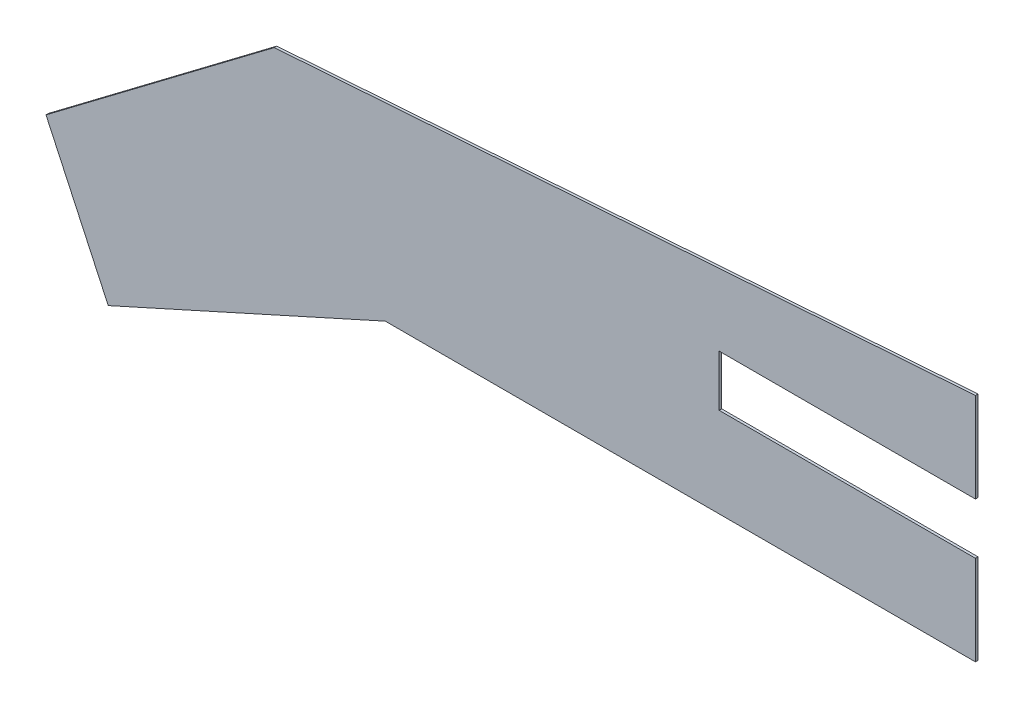
SolidWorks part; units mm, degrees
ref_plane "Alzado" through (0, 0, 0) normal (0, 0, 1) x (1, 0, 0)
ref_plane "Planta" through (0, 0, 0) normal (0, 1, 0) x (1, 0, 0)
ref_plane "Vista lateral" through (0, 0, 0) normal (1, 0, 0) x (0, 0, -1)
sketch "Model" plane through (0, 0, 0) normal (0, 0, 1) x (1, 0, 0)
  line L0 (62.5482, 15.9319) -> (51.5388, 15.9319)
  line L1 (1.1216, 15.9319) -> (1.3716, 15.9319)
  line L2 (51.5388, 15.9319) -> (39.5294, 15.9319)
  line L3 (28.7227, 11.0548) -> (26.2951, 16.2834)
  line L4 (39.5294, 15.9319) -> (28.7227, 11.0548)
  line L5 (52.5482, 19.4319) -> (62.5482, 19.4319)
  line L6 (52.5482, 21.4319) -> (52.5482, 19.4319)
  line L7 (62.5482, 21.4319) -> (52.5482, 21.4319)
  line L8 (62.5482, 24.9319) -> (62.5482, 21.4319)
  line L9 (35.1968, 23.0071) -> (26.2951, 16.2834)
  line L10 (62.5482, 24.9319) -> (35.1968, 23.0071)
  line L11 (35.1968, 23.0071) -> (62.5482, 24.9319)
  line L12 (62.5482, 19.4319) -> (62.5482, 15.9319)
extrude "Saliente-Extruir1" add sketch "Model" along normal blind 0.1 contours L12 L5 L6 L7 L8 L10 L9 L3 L4 L2 L0
